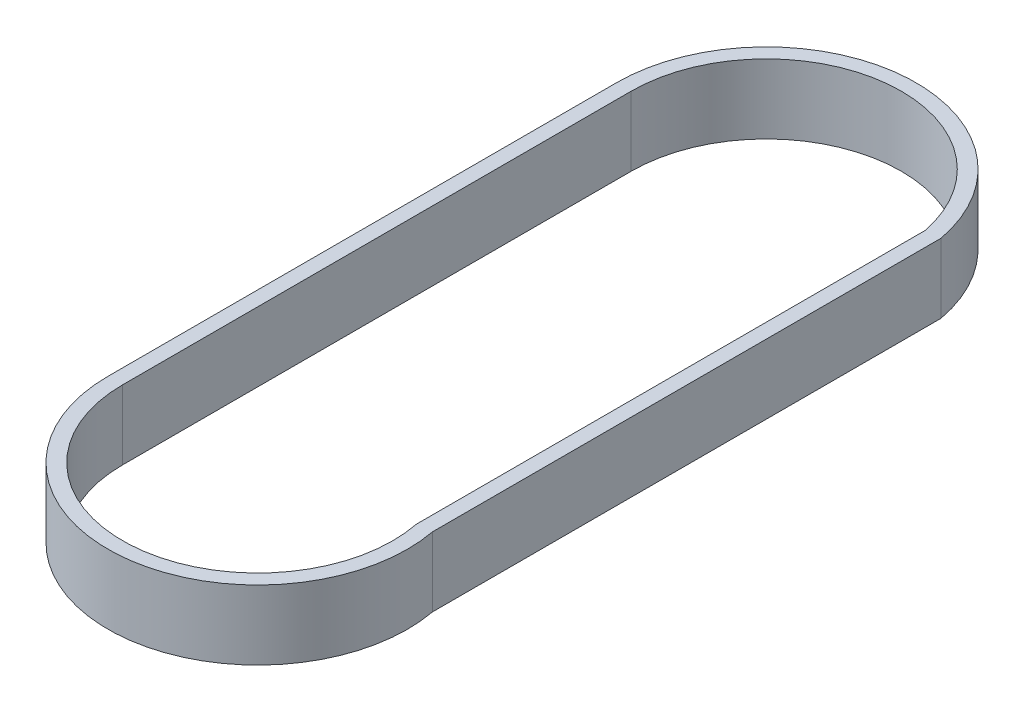
SolidWorks part; units mm, degrees
ref_plane "Front Plane" through (0, 0, 0) normal (0, 0, 1) x (1, 0, 0)
ref_plane "Top Plane" through (0, 0, 0) normal (0, 1, 0) x (1, 0, 0)
ref_plane "Right Plane" through (0, 0, 0) normal (1, 0, 0) x (0, 0, -1)
sketch "Sketch1" plane through (0, 0, 0) normal (0, 1, 0) x (1, 0, 0)
  line L0 (0, 52.082) -> (0, -57.9)
  line L1 (57.8677, -52.2465) -> (57.8677, 57.7355)
  line L2 (61.0427, -51.9444) -> (61.0427, 58.0376)
  line L3 (-3.175, 52.082) -> (-3.175, -57.9)
  arc A0 (0, 52.082) -> (57.8677, 57.7355) centre (29.21, 52.082) cw
  arc A1 (0, -57.9) -> (57.8677, -52.2465) centre (29.21, -57.9) ccw
  arc A2 (-3.175, 52.082) -> (61.0427, 58.0376) centre (29.21, 52.082) cw
  arc A3 (-3.175, -57.9) -> (61.0427, -51.9444) centre (29.21, -57.9) ccw
  dimension "D1" = 109.982
  dimension "D2" = 29.21
  dimension "D3" = 3.175
extrude "Boss-Extrude1" add sketch "Sketch1" along normal blind 15
